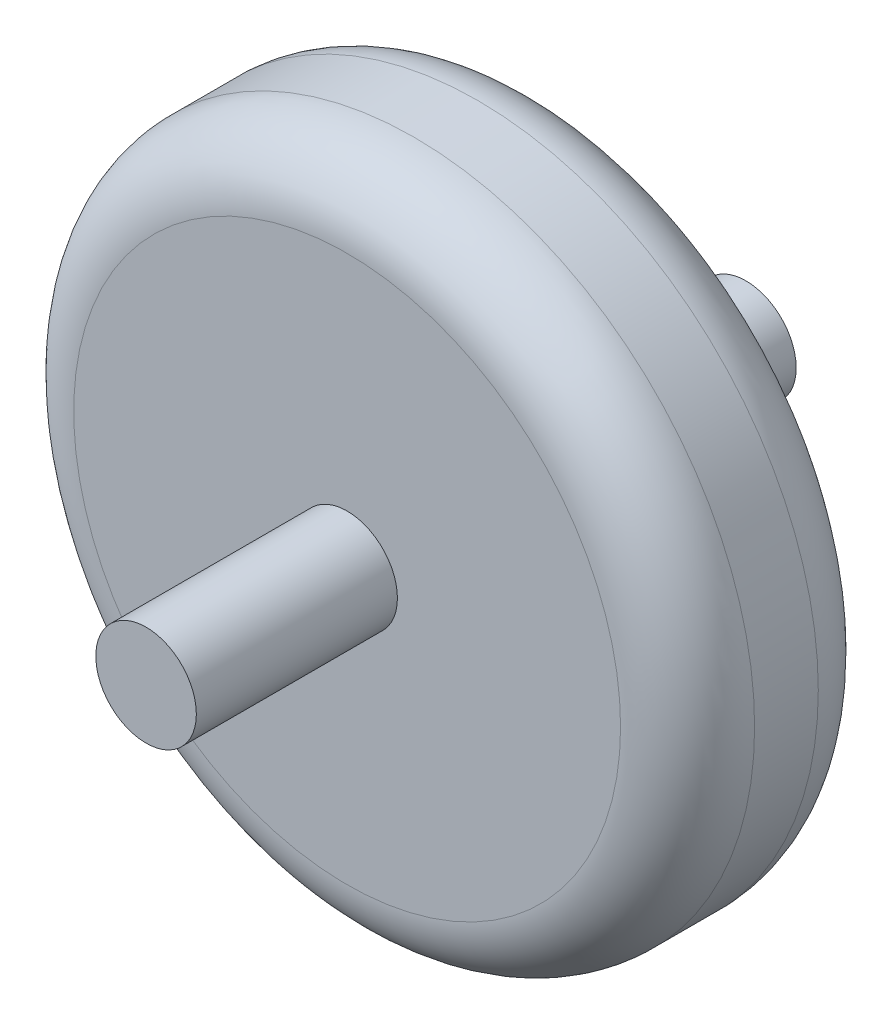
SolidWorks part; units mm, degrees
ref_plane "Front Plane" through (0, 0, 0) normal (0, 0, 1) x (1, 0, 0)
ref_plane "Top Plane" through (0, 0, 0) normal (0, 1, 0) x (1, 0, 0)
ref_plane "Right Plane" through (0, 0, 0) normal (1, 0, 0) x (0, 0, -1)
sketch "Sketch1" plane through (0, 0, 0) normal (0, 0, 1) x (1, 0, 0)
  circle A0 centre (0, 0) radius 101.6
  dimension "D1" = 203.2
extrude "Boss-Extrude1" add sketch "Sketch1" along normal blind 59
fillet "Fillet1" radius 20 2 edges at (101.6, 0, 59) (101.6, 0, 0)
sketch "Sketch2" plane through (0, 0, 59) normal (0, 0, 1) x (1, 0, 0)
  circle A0 centre (0, 0) radius 15
  dimension "D1" = 30
extrude "Boss-Extrude2" add sketch "Sketch2" along normal blind 60 and the other way blind 119
